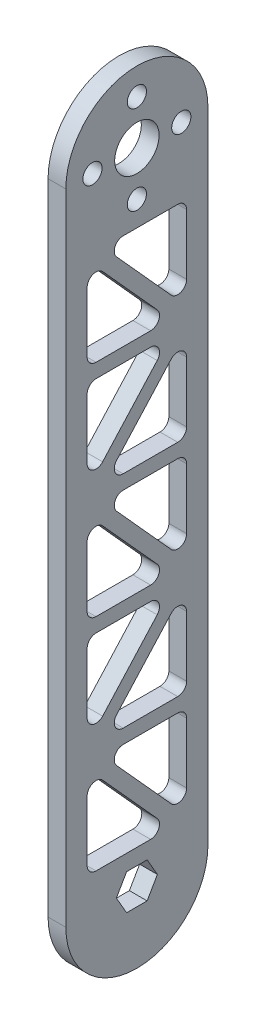
SolidWorks part; units mm, degrees
ref_plane "Front Plane" through (0, 0, 0) normal (0, 0, 1) x (1, 0, 0)
ref_plane "Top Plane" through (0, 0, 0) normal (0, 1, 0) x (1, 0, 0)
ref_plane "Right Plane" through (0, 0, 0) normal (1, 0, 0) x (0, 0, -1)
sketch "Sketch1" plane through (0, 0, 0) normal (1, 0, 0) x (0, 0, -1)
  line L0 (0, 0) -> (0, 228.6) construction
  line L1 (7.3323, 0) -> (3.6662, 6.35)
  line L2 (3.6662, 6.35) -> (-3.6662, 6.35)
  line L3 (-3.6662, 6.35) -> (-7.3323, 0)
  line L4 (-7.3323, 0) -> (-3.6662, -6.35)
  line L5 (-3.6662, -6.35) -> (3.6662, -6.35)
  line L6 (3.6662, -6.35) -> (7.3323, 0)
  line L7 (0, 55) -> (0, -55) construction
  line L8 (0, 228.6) -> (0, 212.725) construction
  line L9 (-25.4, 228.6) -> (-25.4, 0)
  line L10 (25.4, 228.6) -> (25.4, 0)
  circle A0 centre (0, 0) radius 6.35 construction
  circle A1 centre (0, 228.6) radius 7.9375
  circle A2 centre (0, 228.6) radius 15.875 construction
  circle A3 centre (0, 212.725) radius 3.429
  circle A4 centre (-15.875, 228.6) radius 3.429
  circle A5 centre (0, 244.475) radius 3.429
  circle A6 centre (15.875, 228.6) radius 3.429
  arc A7 (25.4, 228.6) -> (-25.4, 228.6) centre (0, 228.6) ccw
  arc A8 (-25.4, 0) -> (25.4, 0) centre (0, 0) ccw
  dimension "D1" = 12.7
  dimension "D3" = 15.875
  dimension "D4" = 31.75
  dimension "D5" = 6.858
  dimension "D8" = 25.4
  dimension "D2" = 228.6
  dimension "D7" = 15.875
  dimension "D6" = 4
extrude "Boss-Extrude1" add sketch "Sketch1" along normal blind 6.35
sketch "Sketch3" plane through (6.35, 0, 0) normal (1, 0, 0) x (0, 0, -1)
  line L0 (17.78, 206.375) -> (17.78, 167.005) construction
  line L1 (-17.78, 206.375) -> (17.78, 167.005) construction
  line L2 (17.78, 167.005) -> (-17.78, 127.635) construction
  line L3 (-17.78, 206.375) -> (17.78, 206.375) construction
  line L4 (-17.78, 9.525) -> (17.78, 9.525) construction
  line L5 (-17.78, 228.6) -> (-17.78, 0)
  line L6 (17.78, 0) -> (17.78, 228.6)
  line L7 (-17.78, 228.6) -> (-17.78, 0)
  line L8 (17.78, 0) -> (17.78, 228.6)
  line L9 (-17.78, 127.635) -> (17.78, 88.265) construction
  line L10 (17.78, 88.265) -> (-17.78, 48.895) construction
  line L11 (-17.78, 48.895) -> (17.78, 9.525) construction
  line L12 (17.78, 167.005) -> (-17.78, 167.005) construction
  line L13 (-17.78, 127.635) -> (17.78, 127.635) construction
  line L14 (17.78, 88.265) -> (-17.78, 88.265) construction
  line L15 (-17.78, 48.895) -> (17.78, 48.895) construction
  line L16 (-23.4969, 208.915) -> (15.8951, 165.3025)
  line L17 (-23.4969, 208.915) -> (17.78, 208.915)
  line L18 (17.78, 164.465) -> (-17.78, 164.465)
  line L19 (19.6649, 165.3025) -> (-15.8951, 125.9325)
  line L20 (-17.78, 130.175) -> (17.78, 130.175)
  line L21 (-15.8951, 129.3375) -> (19.6649, 89.9675)
  line L22 (17.78, 85.725) -> (-17.78, 85.725)
  line L23 (19.6649, 86.5625) -> (-15.8951, 47.1925)
  line L24 (-17.78, 51.435) -> (17.78, 51.435)
  line L25 (-15.8951, 50.5975) -> (23.4969, 6.985)
  line L26 (-17.78, 6.985) -> (23.4969, 6.985)
  line L27 (-12.0631, 203.835) -> (19.6649, 168.7075)
  line L28 (-12.0631, 203.835) -> (17.78, 203.835)
  line L29 (17.78, 169.545) -> (-17.78, 169.545)
  line L30 (15.8951, 168.7075) -> (-19.6649, 129.3375)
  line L31 (-17.78, 125.095) -> (17.78, 125.095)
  line L32 (-19.6649, 125.9325) -> (15.8951, 86.5625)
  line L33 (17.78, 90.805) -> (-17.78, 90.805)
  line L34 (15.8951, 89.9675) -> (-19.6649, 50.5975)
  line L35 (-17.78, 46.355) -> (17.78, 46.355)
  line L36 (-19.6649, 47.1925) -> (12.0631, 12.065)
  line L37 (-17.78, 12.065) -> (12.0631, 12.065)
  circle A4 centre (0, 212.725) radius 3.429 construction
  arc A6 (-17.78, 0) -> (17.78, 0) centre (0, 0) ccw
  arc A7 (17.78, 228.6) -> (-17.78, 228.6) centre (0, 228.6) ccw
  arc A8 (-17.78, 0) -> (17.78, 0) centre (0, 0) ccw
  arc A9 (17.78, 228.6) -> (-17.78, 228.6) centre (0, 228.6) ccw
  dimension "D2" = 6.35
  dimension "D3" = 9.525
  dimension "D4" = 42.089
  dimension "D5" = 42.089
  dimension "D6" = 42.089
  dimension "D7" = 42.089
  dimension "D8" = 2.54
  dimension "D1" = 7.62
  dimension "D9" = 2.54
extrude "Cut-Extrude2" cut sketch "Sketch3" against normal through all contours L28 L27 L8 | L29 L16 L7 | L30 L18 L7 | L19 L20 L8 | L33 L32 L7 | L31 L21 L8 | L23 L24 L8 | L34 L22 L7 | L35 L25 L8 | L7 L37 L36
fillet "Fillet2" radius 3.175 30 edges at (3.175, 12.065, 17.78) (3.175, 12.065, -12.0631) (3.175, 45.1056, 17.78) (3.175, 46.355, 12.0631) (3.175, 13.3144, -17.78) (3.175, 46.355, -17.78) (3.175, 85.725, -12.0631) (3.175, 85.725, 17.78) (3.175, 52.6844, 17.78) (3.175, 51.435, 12.0631) (3.175, 51.435, -17.78) (3.175, 84.4756, -17.78) (3.175, 125.095, 12.0631) (3.175, 92.0544, -17.78) (3.175, 125.095, -17.78) (3.175, 90.805, -12.0631) (3.175, 123.8456, 17.78) (3.175, 90.805, 17.78) (3.175, 130.175, 12.0631) (3.175, 130.175, -17.78) (3.175, 163.2156, -17.78) (3.175, 164.465, -12.0631) (3.175, 164.465, 17.78) (3.175, 131.4244, 17.78) (3.175, 169.545, -12.0631) (3.175, 169.545, 17.78) (3.175, 203.835, 12.0631) (3.175, 170.7944, -17.78) (3.175, 203.835, -17.78) (3.175, 202.5856, 17.78)
